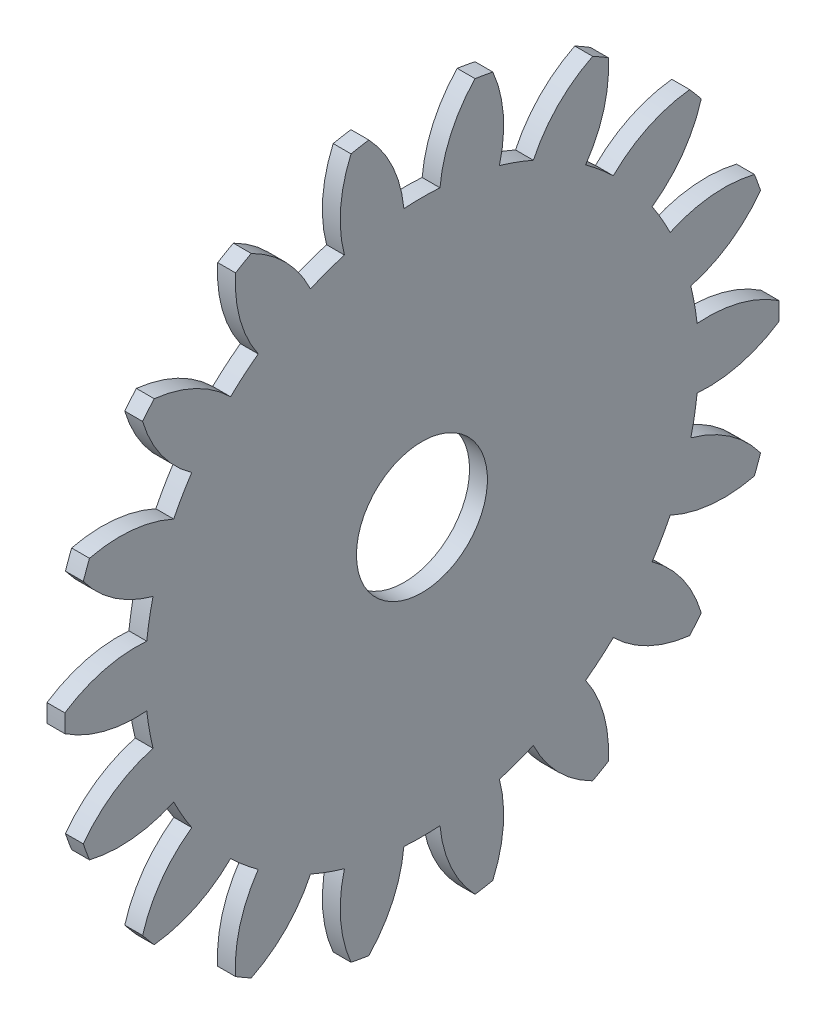
SolidWorks part; units mm, degrees
ref_plane "Plane1" through (0, 0, 0) normal (0, 0, 1) x (1, 0, 0)
ref_plane "Plane2" through (0, 0, 0) normal (0, 1, 0) x (1, 0, 0)
ref_plane "Plane3" through (0, 0, 0) normal (1, 0, 0) x (0, 0, -1)
other "Configuration Table"
sketch "HoldingSke" plane through (0, 0, 0) normal (0, 1, 0) x (1, 0, 0)
  line L0 (0, 0) -> (0.1585, -0.0515)
  line L1 (-15, 0) -> (100, 0) construction
  line L2 (0, 0) -> (-2.1039, 2.3779)
  line L3 (0, 0) -> (-11.863, 4.5341)
  line L4 (0, 0) -> (8.2133, 2.6687)
  line L5 (0, 0) -> (-46.8476, -17.4728)
  line L6 (0, 0) -> (-2.4869, -1.6779)
  line L7 (-2.1039, 2.3779) -> (8.6586, 51.2059)
  line L8 (-76.2, 54.61) -> (-72.9, 54.61)
  line L9 (-71.009, 38.7566) -> (-53.1078, 45.2721)
  line L10 (-76.2, 71.12) -> (104.1128, 71.12)
  line L11 (0, 0) -> (-3, 0)
  line L12 (-76.2, 101.6) -> (-75.993, 101.6)
  line L13 (24.9733, 27.94) -> (52.9518, 28.4284)
  line L14 (24.9733, 27.94) -> (24.9743, 27.94)
  line L15 (24.9733, 27.94) -> (100.4006, 29.5858)
  line L16 (-63.627, -6) -> (-12.827, -6)
  circle A0 centre (0, 0) radius 11
  circle A1 centre (0, 0) radius 37.5
  circle A2 centre (0, 0) radius 37.5
  circle A3 centre (0, 0) radius 11
  dimension "MHD" = 75
  dimension "Hub_dia" = 75
  dimension "Bore" = 22
  dimension "MBD" = 22
  dimension "Num_teeth" = 18
  dimension "Pitch" = 0.1667
  dimension "Overall_len" = 50
  dimension "Show_teeth" = 18
  dimension "Thickness" = 3
  dimension "OAL" = 50.0001
  dimension "T_dim" = 3.3
  dimension "Ap" = 20
  dimension "H" = 19.05
  dimension "Pitch_radius" = 180.3128
  dimension "Width" = 3
  dimension "Backlash" = 0.207
  dimension "Addendum_fac" = 1
  dimension "Dedendum_fac" = 1.25
  dimension "Clearance_fac" = 0.25
  dimension "Dedendum_add" = 0.001
  dimension "Module" = 6
sketch "BasProSke" plane through (0, 0, 0) normal (0, 1, 0) x (1, 0, 0)
  line L0 (-10, 0) -> (60, 0) construction
  line L1 (0, 0) -> (0, 60)
  line L2 (0, 0) -> (3, 0)
  line L3 (3, 0) -> (3, 60)
  line L4 (3, 60) -> (0, 60)
  dimension "Thickness" = 3
  dimension "Diameter" = 120
revolve "Base-Revolve" add sketch "BasProSke" angle 360 about L0
sketch "TooCutSke" plane through (0, 0, 0) normal (1, 0, 0) x (0, 0, -1)
  line L1 (0, 0) -> (0, 107) construction
  line L2 (0, 0) -> (-5.0684, 53.7616) construction
  line L3 (0, 0) -> (-18.6932, 106.0145) construction
  line L4 (-5.0684, 53.7616) -> (-9.3466, 53.0073) construction
  arc A0 (3.0326, 46.4) -> (-3.0326, 46.4) centre (0, 0) ccw
  arc A1 (8.9425, 59.3555) -> (-8.9425, 59.3555) centre (0, 0) ccw
  circle A2 centre (0, 0) radius 54 construction
  circle A3 centre (0, 0) radius 50.7434 construction
  arc A4 (-3.0326, 46.4) -> (-8.9425, 59.3555) centre (-24.5412, 44.4142) ccw
  arc A5 (8.9425, 59.3555) -> (3.0326, 46.4) centre (24.5412, 44.4142) ccw
  dimension "Root_dia" = 92.998
  dimension "Overcut_dia" = 120.0508
  dimension "Pitch_dia" = 108
  dimension "Base_dia" = 101.4868
  dimension "Flank_rad" = 21.6
  dimension "Half_ang" = 10
  dimension "Half_CT" = 4.3442
extrude "ToothCut" cut sketch "TooCutSke" along normal through all
fillet "Breaks" [suppressed] radius 0.12
fillet "RootFillets" [suppressed] radius 1.501
pattern_circular "TeethCuts" count 18 every 20 about axis through (-10, 0, 0) along (1, 0, 0) of "ToothCut", "RootFillets", "Breaks"
sketch "HubNeaOneSke" plane through (0, 0, 0) normal (-1, 0, 0) x (0, 0, 1)
  circle A0 centre (0, 0) radius 37.5
  dimension "Diameter" = 75
extrude "HubNearOne" [suppressed] add sketch "HubNeaOneSke" along normal blind 47.0001
sketch "HubNeaBotSke" plane through (0, 0, 0) normal (-1, 0, 0) x (0, 0, 1)
  circle A0 centre (0, 0) radius 37.5
  dimension "Diameter" = 75
extrude "HubNearBoth" [suppressed] add sketch "HubNeaBotSke" along normal blind 23.5
ref_plane "FarPln" through (3, 0, 0) normal (1, 0, 0) x (0, 0, -1)
sketch "HubFarSke" plane through (3, 0, 0) normal (1, 0, 0) x (0, 0, -1)
  circle A0 centre (0, 0) radius 37.5
  dimension "Diameter" = 75
extrude "HubFar" [suppressed] add sketch "HubFarSke" along normal blind 23.5
sketch "BorSke" plane through (0, 0, 0) normal (1, 0, 0) x (0, 0, -1)
  circle A0 centre (0, 0) radius 11
  dimension "Diameter" = 22
extrude "Bore" cut sketch "BorSke" along normal mid plane 100.0001
sketch "KeySke" plane through (0, 0, 0) normal (1, 0, 0) x (0, 0, -1)
  line L0 (-4, 0) -> (-4, 14.3)
  line L1 (-4, 14.3) -> (4, 14.3)
  line L2 (4, 14.3) -> (4, 0)
  line L3 (0, 0) -> (0, 34) construction
  line L4 (-4, 0) -> (4, 0)
  dimension "Offset" = 14.3
  dimension "Width" = 8
extrude "Keyway" [suppressed] cut sketch "KeySke" along normal mid plane 100.0001
pattern_circular "Keyway2" [suppressed] count 2 every 90 about axis through (-10, 0, 0) along (1, 0, 0)
sketch "Sketch1" plane through (3, 0, 0) normal (1, 0, 0) x (0, 0, -1)
  circle A0 centre (0, 0) radius 53.3151
equation "' \"Module@HoldingSke\" = 6.35"
equation "' \"Num_teeth@HoldingSke\" = 12"
equation "' \"Ap@HoldingSke\" =  20"
equation "' \"Ap@HoldingSke\" = 20"
equation "' \"Width@HoldingSke\" = 0.5 * 25.4"
equation "' \"Hub_dia@HoldingSke\"= 1 * 25.4"
equation "' \"Hub_dia@HoldingSke\" = 1 * 25.4"
equation "' \"Overall_len@HoldingSke\" = 1.0 * 25.4"
equation "' \"Bore@HoldingSke\" = 0.75 * 25.4"
equation "' \"T_dim@HoldingSke\" = 0.1 * 25.4"
equation "' \"Width@KeySke\" = 0.25 * 25.4"
equation "' \"Show_teeth@HoldingSke\" = 13"
equation "' \"Backlash@HoldingSke\" = 0.009 * 25.4"
equation "' \"Addendum_fac@HoldingSke\" = 1.0"
equation "' \"Dedendum_fac@HoldingSke\" = 1.25"
equation "' \"Dedendum_add@HoldingSke\" = 0.00005 * 25.4"
equation "' \"Clearance_fac@HoldingSke\" = 0.25"
equation "\"Pitch@HoldingSke\" = 1 / \"Module@HoldingSke\""
equation "\"Overcut_dia@TooCutSke\" = (\"Num_teeth@HoldingSke\" + 2 * \"Addendum_fac@HoldingSke\") / \"Pitch@HoldingSke\" + 0.002 * 25.4"
equation "\"Pitch_dia@TooCutSke\" = \"Num_teeth@HoldingSke\" / \"Pitch@HoldingSke\""
equation "\"Base_dia@TooCutSke\" = \"Num_teeth@HoldingSke\" / \"Pitch@HoldingSke\" * cos((\"Ap@HoldingSke\"  * 3.14159265 / 180))"
equation "\"Root_dia@TooCutSke\" = (\"Num_teeth@HoldingSke\" + 2) / \"Pitch@HoldingSke\" - 2 * (\"Addendum_fac@HoldingSke\" + \"Dedendum_fac@HoldingSke\") / \"Pitch@HoldingSke\" - \"Dedendum_add@HoldingSke\" * 2"
equation "\"Half_ang@TooCutSke\" = 180 / \"Num_teeth@HoldingSke\""
equation "\"Half_CT@TooCutSke\" = \"Num_teeth@HoldingSke\" / \"Pitch@HoldingSke\" * sin((3.14159265 / 2 / \"Num_teeth@HoldingSke\")) / 2 - 7 * \"Backlash@HoldingSke\" / 4"
equation "\"Flank_rad@TooCutSke\" = \"Num_teeth@HoldingSke\" / \"Pitch@HoldingSke\" / 5"
equation "\"Radius@RootFillets\" = \"Clearance_fac@HoldingSke\" / \"Pitch@HoldingSke\" + \"Dedendum_add@HoldingSke\""
equation "\"Break_rad@Breaks\" = 0.02 / \"Pitch@HoldingSke\""
equation "\"Thickness@HoldingSke\" = \"Width@HoldingSke\""
equation "\"OAL@HoldingSke\" = \"Thickness@HoldingSke\""
equation "\"MHD@HoldingSke\" = (\"Num_teeth@HoldingSke\" + 2) / \"Pitch@HoldingSke\" - 2 * (\"Addendum_fac@HoldingSke\" + \"Dedendum_fac@HoldingSke\")  / \"Pitch@HoldingSke\" - \"Dedendum_add@HoldingSke\" * 2"
equation "\"MBD@HoldingSke\" = (\"Num_teeth@HoldingSke\" + 2) / \"Pitch@HoldingSke\" - 2 * (\"Addendum_fac@HoldingSke\" + \"Dedendum_fac@HoldingSke\")  / \"Pitch@HoldingSke\" - \"Dedendum_add@HoldingSke\" * 2 - 0.002 * 25.4"
equation "\"MHD@HoldingSke\" = ((sgn( \"MHD@HoldingSke\" - \"Hub_dia@HoldingSke\" )-1)*( \"MHD@HoldingSke\" - \"Hub_dia@HoldingSke\" ))/-2+ \"Hub_dia@HoldingSke\""
equation "\"MBD@HoldingSke\" = ((sgn( \"MBD@HoldingSke\" - \"Bore@HoldingSke\" )-1)*( \"MBD@HoldingSke\" - \"Bore@HoldingSke\" ))/-2+ \"Bore@HoldingSke\""
equation "\"OAL@HoldingSke\" = ((sgn( \"OAL@HoldingSke\" - \"Overall_len@HoldingSke\" )+1)*( \"OAL@HoldingSke\" - \"Overall_len@HoldingSke\" ))/2 + \"Overall_len@HoldingSke\" + 0.000002 * 25.4"
equation "\"Num_teeth@TeethCuts\" = int( \"Show_teeth@HoldingSke\" ) + 1"
equation "\"Num_teeth@TeethCuts\" = ((sgn( \"Num_teeth@TeethCuts\" - \"Num_teeth@HoldingSke\" )-1)*( \"Num_teeth@TeethCuts\" - \"Num_teeth@HoldingSke\" ))/-2+ \"Num_teeth@HoldingSke\""
equation "\"Num_teeth@TeethCuts\" = ((sgn( \"Num_teeth@TeethCuts\" - 2.0)+1)*( \"Num_teeth@TeethCuts\" - 2.0))/2 +2.0"
equation "\"Angle@TeethCuts\" = 360.0 / \"Num_teeth@HoldingSke\""
equation "\"Diameter@BasProSke\" = (\"Num_teeth@HoldingSke\" + 2 * \"Addendum_fac@HoldingSke\") / \"Pitch@HoldingSke\""
equation "\"Thickness@BasProSke\"  = \"Thickness@HoldingSke\""
equation "' \"Fillet_rad@BasProSke\" =  \"Thickness@HoldingSke\" * 0.05"
equation "' \"Fillet_rad@BasProSke\" = \"Thickness@HoldingSke\" * 0.05"
equation "\"MHD@HoldingSke\" = ((sgn( \"MHD@HoldingSke\" - \"Root_dia@TooCutSke\" )-1)*( \"MHD@HoldingSke\" - \"Root_dia@TooCutSke\" ))/-2+ \"Root_dia@TooCutSke\""
equation "\"Diameter@HubNeaOneSke\" = \"MHD@HoldingSke\""
equation "\"Length@HubNearOne\" = \"OAL@HoldingSke\" - \"Thickness@BasProSke\""
equation "\"Diameter@HubNeaBotSke\" = \"MHD@HoldingSke\""
equation "\"Length@HubNearBoth\" = ( \"OAL@HoldingSke\" - \"Thickness@BasProSke\" ) / 2.0"
equation "\"Thickness@FarPln\" = \"Thickness@BasProSke\""
equation "\"Diameter@HubFarSke\" = \"MHD@HoldingSke\""
equation "\"Length@HubFar\" = ( \"OAL@HoldingSke\" - \"Thickness@BasProSke\" ) / 2.0"
equation "\"Diameter@BorSke\" = \"MBD@HoldingSke\""
equation "\"D1@Bore\" = \"OAL@HoldingSke\" * 2.0"
equation "\"D1@Keyway\" = \"OAL@HoldingSke\" * 2.0"
equation "\"Offset@KeySke\" = \"T_dim@HoldingSke\" + \"MBD@HoldingSke\" / 2.0"
